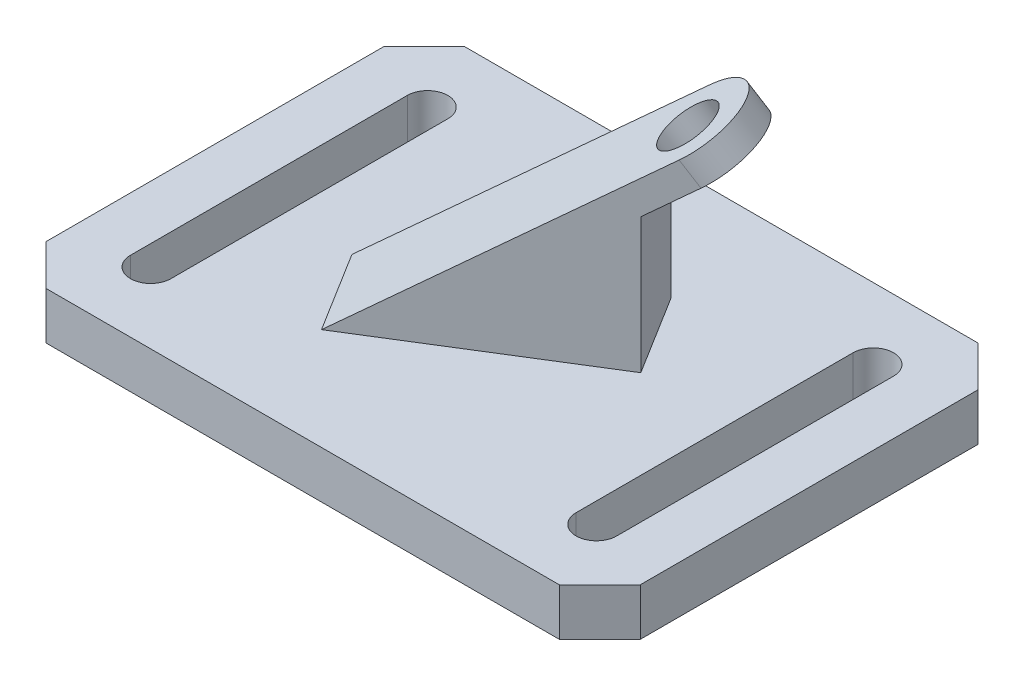
SolidWorks part; units mm, degrees
ref_plane "Front Plane" through (0, 0, 0) normal (0, 0, 1) x (1, 0, 0)
ref_plane "Top Plane" through (0, 0, 0) normal (0, 1, 0) x (1, 0, 0)
ref_plane "Right Plane" through (0, 0, 0) normal (1, 0, 0) x (0, 0, -1)
sketch "Sketch1" plane through (0, 0, 0) normal (0, 1, 0) x (1, 0, 0)
  line L0 (-44, 25) -> (-38, 31)
  line L1 (-38, 31) -> (38, 31)
  line L2 (-44, 25) -> (-44, -25)
  line L3 (-38, -31) -> (38, -31)
  line L4 (44, 25) -> (44, -25)
  line L5 (-44, 31) -> (44, -31) construction
  line L6 (-44, -31) -> (44, 31) construction
  line L7 (-44, -25) -> (-38, -31)
  line L8 (38, 31) -> (44, 25)
  line L9 (38, -31) -> (44, -25)
  line L10 (-33, -20.5) -> (-33, 20.5) construction
  line L11 (-36, -20.5) -> (-36, 20.5)
  line L12 (-30, -20.5) -> (-30, 20.5)
  line L13 (33, -20.5) -> (33, 20.5) construction
  line L14 (30, -20.5) -> (30, 20.5)
  line L15 (36, -20.5) -> (36, 20.5)
  arc A0 (-36, -20.5) -> (-30, -20.5) centre (-33, -20.5) ccw
  arc A1 (-30, 20.5) -> (-36, 20.5) centre (-33, 20.5) ccw
  arc A2 (30, -20.5) -> (36, -20.5) centre (33, -20.5) ccw
  arc A3 (36, 20.5) -> (30, 20.5) centre (33, 20.5) ccw
  point P0 (0, 0)
  point P16 (-33, 0)
  point P23 (33, 0)
  dimension "D1" = 62
  dimension "D2" = 88
  dimension "D3" = 8
  dimension "D4" = 6
  dimension "D9" = 6
  dimension "D10" = 8
  dimension "D11" = 41
  dimension "D12" = 41
  dimension "D13" = 10.5
  dimension "D14" = 10.5
extrude "Boss-Extrude1" add sketch "Sketch1" along normal blind 7
sketch "Sketch2" plane through (0, 7, 0) normal (0, 1, 0) x (1, 0, 0)
  line L0 (0, 0) -> (33, 20.5) construction
  line L1 (33, 20.5) -> (-33, -20.5) construction
  line L2 (-19.6454, -4.0961) -> (-12.3102, -15.9039) construction
  dimension "D1" = 20
  dimension "D2" = 90
ref_plane "Plane1" through (-8.3593, 13.5448, 5.1929) normal (-0.4993, 0.809, 0.3102) x (0.5277, 0, 0.8494)
sketch "Sketch3" plane through (-8.3593, 13.5448, 5.1929) normal (-0.4993, 0.809, 0.3102) x (0.5277, 0, 0.8494)
  line L0 (-7, -11.1347) -> (7, -11.1347) construction
  line L2 (0, 35.5441) -> (0, -27.3151) construction
  line L3 (-6.8872, -11.1347) -> (7.0135, -11.1347) construction
  point P3 (0, -11.1347)
  dimension "D1" = 14
ref_plane "Plane2" through (0, 0, 0) normal (-0.5277, 0, -0.8494) x (-0.8494, 0, 0.5277)
sketch "Sketch4" plane through (0, 0, 0) normal (-0.5277, 0, -0.8494) x (-0.8494, 0, 0.5277)
  line L0 (18.8491, 7) -> (12.5118, 7)
  line L1 (-38.8491, 7) -> (38.8491, 7) construction
  line L2 (-15.4838, 27) -> (-27.619, 35.8168)
  line L3 (-27.619, 35.8168) -> (-25.2679, 39.0528)
  line L4 (-25.2679, 39.0528) -> (18.8491, 7)
  line L5 (18.8491, 7) -> (32.438, 7) construction
  line L6 (-15.4838, 27) -> (-15.4838, 7)
  line L7 (-15.4838, 7) -> (12.5118, 7)
  dimension "D1" = 36
  dimension "D2" = 4
  dimension "D3" = 20
  dimension "D4" = 15
extrude "Boss-Extrude2" add sketch "Sketch4" along normal mid plane 14
sketch "Sketch6" plane through (-8.3593, 13.5448, 5.1929) normal (-0.4993, 0.809, 0.3102) x (0.8664, 0.4662, 0.1787)
  line L0 (30.157, 31.9819) -> (24.6049, 27.7187) construction
  line L2 (24.6049, 27.7187) -> (30.157, 31.9819) construction
  line L3 (30.157, 31.9819) -> (38.6834, 20.8778) construction
  line L4 (38.6834, 20.8778) -> (33.1313, 16.6146) construction
  line L6 (24.6049, 27.7187) -> (30.157, 31.9819)
  line L7 (30.157, 31.9819) -> (34.4202, 26.4299)
  line L8 (34.4202, 26.4299) -> (38.6834, 20.8778)
  line L9 (38.6834, 20.8778) -> (33.1313, 16.6146)
  arc A0 (33.1313, 16.6146) -> (24.6049, 27.7187) centre (28.8681, 22.1667) ccw
  line M4 (-4.5683, -12.3334) -> (38.6834, 20.8778)
  line M5 (38.6834, 20.8778) -> (30.157, 31.9819)
  line M6 (30.157, 31.9819) -> (-13.0947, -1.2293)
  dimension "D2" = 14
  dimension "D1" = 7
extrude "Cut-Extrude1" cut sketch "Sketch6" against normal blind 14 contours A0 M5 M6 | A0 M4 M5
sketch "Sketch7" plane through (-8.3593, 13.5448, 5.1929) normal (-0.4993, 0.809, 0.3102) x (0.8664, 0.4662, 0.1787)
  circle A0 centre (28.1917, 21.6473) radius 4
  dimension "D1" = 8
extrude "Cut-Extrude2" cut sketch "Sketch7" against normal blind 14
